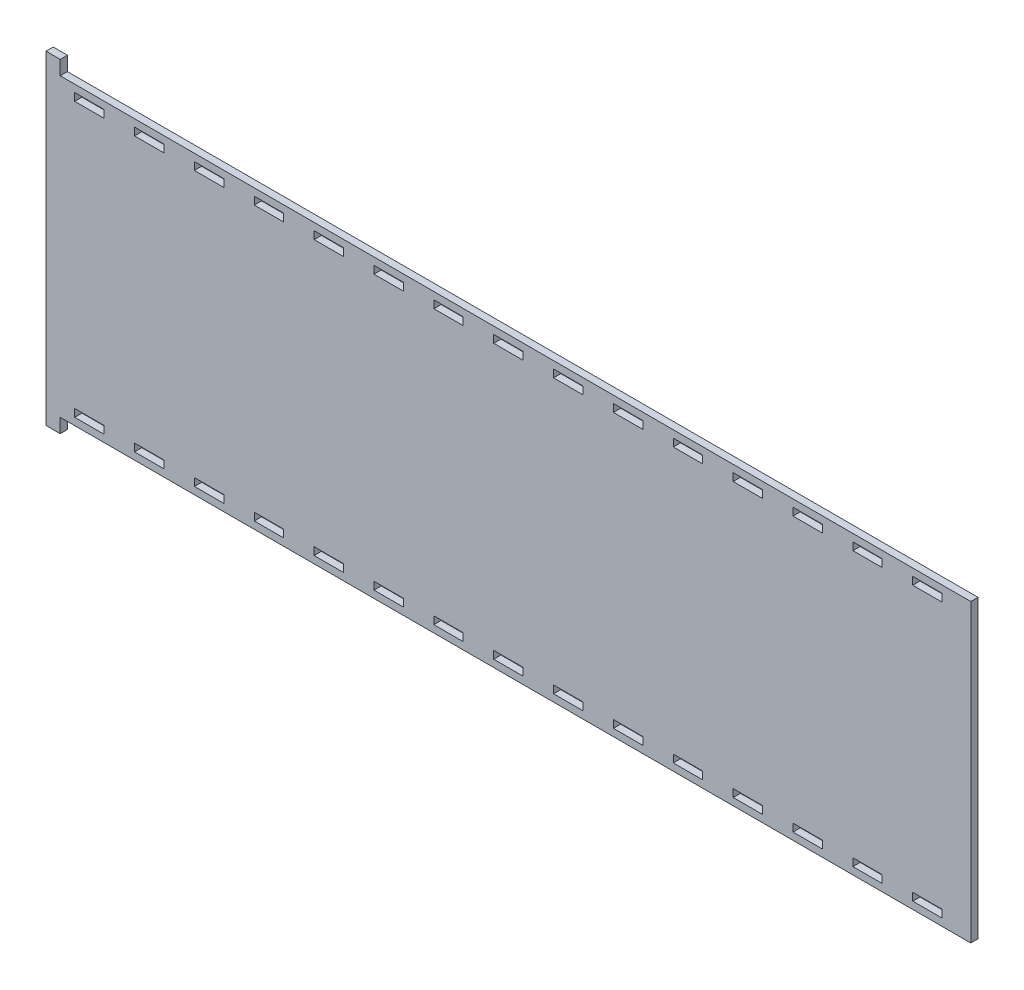
SolidWorks part; units mm, degrees
ref_plane "Front Plane" through (0, 0, 0) normal (0, 0, 1) x (1, 0, 0)
ref_plane "Top Plane" through (0, 0, 0) normal (0, 1, 0) x (1, 0, 0)
ref_plane "Right Plane" through (0, 0, 0) normal (1, 0, 0) x (0, 0, -1)
sketch "Sketch1" plane through (0, 0, 0) normal (0, 0, 1) x (1, 0, 0)
  line L8 (25.5, 123.5218) -> (12.6, 123.5218)
  line L9 (25.5, 120.1436) -> (25.5, 123.5218)
  line L10 (12.6, 120.1436) -> (25.5, 120.1436)
  line L11 (12.6, 123.5218) -> (12.6, 120.1436)
  line L16 (51.8071, 123.5218) -> (38.9071, 123.5218)
  line L17 (51.8071, 120.1436) -> (51.8071, 123.5218)
  line L18 (38.9071, 120.1436) -> (51.8071, 120.1436)
  line L19 (38.9071, 123.5218) -> (38.9071, 120.1436)
  line L24 (393.8, 123.5218) -> (380.9, 123.5218)
  line L25 (393.8, 120.1436) -> (393.8, 123.5218)
  line L26 (380.9, 120.1436) -> (393.8, 120.1436)
  line L27 (380.9, 123.5218) -> (380.9, 120.1436)
  line L32 (367.4929, 123.5218) -> (354.5929, 123.5218)
  line L33 (367.4929, 120.1436) -> (367.4929, 123.5218)
  line L34 (354.5929, 120.1436) -> (367.4929, 120.1436)
  line L35 (354.5929, 123.5218) -> (354.5929, 120.1436)
  line L40 (78.1143, 123.5218) -> (65.2143, 123.5218)
  line L41 (78.1143, 120.1436) -> (78.1143, 123.5218)
  line L42 (65.2143, 120.1436) -> (78.1143, 120.1436)
  line L43 (65.2143, 123.5218) -> (65.2143, 120.1436)
  line L48 (104.4214, 123.5218) -> (91.5214, 123.5218)
  line L49 (104.4214, 120.1436) -> (104.4214, 123.5218)
  line L50 (91.5214, 120.1436) -> (104.4214, 120.1436)
  line L51 (91.5214, 123.5218) -> (91.5214, 120.1436)
  line L56 (130.7286, 123.5218) -> (117.8286, 123.5218)
  line L57 (130.7286, 120.1436) -> (130.7286, 123.5218)
  line L58 (117.8286, 120.1436) -> (130.7286, 120.1436)
  line L59 (117.8286, 123.5218) -> (117.8286, 120.1436)
  line L64 (157.0357, 123.5218) -> (144.1357, 123.5218)
  line L65 (157.0357, 120.1436) -> (157.0357, 123.5218)
  line L66 (144.1357, 120.1436) -> (157.0357, 120.1436)
  line L67 (144.1357, 123.5218) -> (144.1357, 120.1436)
  line L72 (183.3429, 123.5218) -> (170.4429, 123.5218)
  line L73 (183.3429, 120.1436) -> (183.3429, 123.5218)
  line L74 (170.4429, 120.1436) -> (183.3429, 120.1436)
  line L75 (170.4429, 123.5218) -> (170.4429, 120.1436)
  line L80 (209.65, 123.5218) -> (196.75, 123.5218)
  line L81 (209.65, 120.1436) -> (209.65, 123.5218)
  line L82 (196.75, 120.1436) -> (209.65, 120.1436)
  line L83 (196.75, 123.5218) -> (196.75, 120.1436)
  line L88 (235.9571, 123.5218) -> (223.0571, 123.5218)
  line L89 (235.9571, 120.1436) -> (235.9571, 123.5218)
  line L90 (223.0571, 120.1436) -> (235.9571, 120.1436)
  line L91 (223.0571, 123.5218) -> (223.0571, 120.1436)
  line L96 (262.2643, 123.5218) -> (249.3643, 123.5218)
  line L97 (262.2643, 120.1436) -> (262.2643, 123.5218)
  line L98 (249.3643, 120.1436) -> (262.2643, 120.1436)
  line L99 (249.3643, 123.5218) -> (249.3643, 120.1436)
  line L104 (288.5714, 123.5218) -> (275.6714, 123.5218)
  line L105 (288.5714, 120.1436) -> (288.5714, 123.5218)
  line L106 (275.6714, 120.1436) -> (288.5714, 120.1436)
  line L107 (275.6714, 123.5218) -> (275.6714, 120.1436)
  line L112 (314.8786, 123.5218) -> (301.9786, 123.5218)
  line L113 (314.8786, 120.1436) -> (314.8786, 123.5218)
  line L114 (301.9786, 120.1436) -> (314.8786, 120.1436)
  line L115 (301.9786, 123.5218) -> (301.9786, 120.1436)
  line L120 (341.1857, 123.5218) -> (328.2857, 123.5218)
  line L121 (341.1857, 120.1436) -> (341.1857, 123.5218)
  line L122 (328.2857, 120.1436) -> (341.1857, 120.1436)
  line L123 (328.2857, 123.5218) -> (328.2857, 120.1436)
  line L128 (380.9, -0.1032) -> (393.8, -0.1032)
  line L129 (380.9, 3.275) -> (380.9, -0.1032)
  line L130 (393.8, 3.275) -> (380.9, 3.275)
  line L131 (393.8, -0.1032) -> (393.8, 3.275)
  line L136 (354.5929, -0.1032) -> (367.4929, -0.1032)
  line L137 (354.5929, 3.275) -> (354.5929, -0.1032)
  line L138 (367.4929, 3.275) -> (354.5929, 3.275)
  line L139 (367.4929, -0.1032) -> (367.4929, 3.275)
  line L144 (328.2857, -0.1032) -> (341.1857, -0.1032)
  line L145 (328.2857, 3.275) -> (328.2857, -0.1032)
  line L146 (341.1857, 3.275) -> (328.2857, 3.275)
  line L147 (341.1857, -0.1032) -> (341.1857, 3.275)
  line L152 (301.9786, -0.1032) -> (314.8786, -0.1032)
  line L153 (301.9786, 3.275) -> (301.9786, -0.1032)
  line L154 (314.8786, 3.275) -> (301.9786, 3.275)
  line L155 (314.8786, -0.1032) -> (314.8786, 3.275)
  line L160 (275.6714, -0.1032) -> (288.5714, -0.1032)
  line L161 (275.6714, 3.275) -> (275.6714, -0.1032)
  line L162 (288.5714, 3.275) -> (275.6714, 3.275)
  line L163 (288.5714, -0.1032) -> (288.5714, 3.275)
  line L168 (249.3643, -0.1032) -> (262.2643, -0.1032)
  line L169 (249.3643, 3.275) -> (249.3643, -0.1032)
  line L170 (262.2643, 3.275) -> (249.3643, 3.275)
  line L171 (262.2643, -0.1032) -> (262.2643, 3.275)
  line L176 (223.0571, -0.1032) -> (235.9571, -0.1032)
  line L177 (223.0571, 3.275) -> (223.0571, -0.1032)
  line L178 (235.9571, 3.275) -> (223.0571, 3.275)
  line L179 (235.9571, -0.1032) -> (235.9571, 3.275)
  line L184 (196.75, -0.1032) -> (209.65, -0.1032)
  line L185 (196.75, 3.275) -> (196.75, -0.1032)
  line L186 (209.65, 3.275) -> (196.75, 3.275)
  line L187 (209.65, -0.1032) -> (209.65, 3.275)
  line L192 (170.4429, -0.1032) -> (183.3429, -0.1032)
  line L193 (170.4429, 3.275) -> (170.4429, -0.1032)
  line L194 (183.3429, 3.275) -> (170.4429, 3.275)
  line L195 (183.3429, -0.1032) -> (183.3429, 3.275)
  line L200 (144.1357, -0.1032) -> (157.0357, -0.1032)
  line L201 (144.1357, 3.275) -> (144.1357, -0.1032)
  line L202 (157.0357, 3.275) -> (144.1357, 3.275)
  line L203 (157.0357, -0.1032) -> (157.0357, 3.275)
  line L208 (117.8286, -0.1032) -> (130.7286, -0.1032)
  line L209 (117.8286, 3.275) -> (117.8286, -0.1032)
  line L210 (130.7286, 3.275) -> (117.8286, 3.275)
  line L211 (130.7286, -0.1032) -> (130.7286, 3.275)
  line L216 (91.5214, -0.1032) -> (104.4214, -0.1032)
  line L217 (91.5214, 3.275) -> (91.5214, -0.1032)
  line L218 (104.4214, 3.275) -> (91.5214, 3.275)
  line L219 (104.4214, -0.1032) -> (104.4214, 3.275)
  line L224 (65.2143, -0.1032) -> (78.1143, -0.1032)
  line L225 (65.2143, 3.275) -> (65.2143, -0.1032)
  line L226 (78.1143, 3.275) -> (65.2143, 3.275)
  line L227 (78.1143, -0.1032) -> (78.1143, 3.275)
  line L232 (38.9071, -0.1032) -> (51.8071, -0.1032)
  line L233 (38.9071, 3.275) -> (38.9071, -0.1032)
  line L234 (51.8071, 3.275) -> (38.9071, 3.275)
  line L235 (51.8071, -0.1032) -> (51.8071, 3.275)
  line L240 (12.6, -0.1032) -> (25.5, -0.1032)
  line L241 (12.6, 3.275) -> (12.6, -0.1032)
  line L242 (25.5, 3.275) -> (12.6, 3.275)
  line L243 (25.5, -0.1032) -> (25.5, 3.275)
  line L256 (6.25, -9.525) -> (6.25, -3.2782)
  line L257 (6.25, -3.2782) -> (406.4, -3.2782)
  line L258 (406.4, -3.2782) -> (406.4, 126.6968)
  line L259 (406.4, 126.6968) -> (6.25, 126.6968)
  line L260 (6.25, 126.6968) -> (6.25, 132.9436)
  line L261 (6.25, 132.9436) -> (0, 132.9436)
  line L262 (0, 132.9436) -> (0, -9.525)
  line L263 (0, -9.525) -> (6.25, -9.525)
extrude "Boss-Extrude2" add sketch "Sketch1" along normal blind 3.175
sketch "DXF" plane through (0, 0, 0) normal (0, 0, 1) x (1, 0, 0)
  line L0 (25.3984, 123.4202) -> (12.7016, 123.4202)
  line L1 (12.7016, 123.4202) -> (12.7016, 120.2452)
  line L2 (12.7016, 120.2452) -> (25.3984, 120.2452)
  line L3 (25.3984, 120.2452) -> (25.3984, 123.4202)
  line L4 (51.7055, 123.4202) -> (39.0087, 123.4202)
  line L5 (39.0087, 123.4202) -> (39.0087, 120.2452)
  line L6 (39.0087, 120.2452) -> (51.7055, 120.2452)
  line L7 (51.7055, 120.2452) -> (51.7055, 123.4202)
  line L8 (25.5, 123.5218) -> (12.6, 123.5218) construction
  line L9 (25.5, 120.1436) -> (25.5, 123.5218) construction
  line L10 (12.6, 120.1436) -> (25.5, 120.1436) construction
  line L11 (12.6, 123.5218) -> (12.6, 120.1436) construction
  line L12 (393.6984, 123.4202) -> (381.0016, 123.4202)
  line L13 (381.0016, 123.4202) -> (381.0016, 120.2452)
  line L14 (381.0016, 120.2452) -> (393.6984, 120.2452)
  line L15 (393.6984, 120.2452) -> (393.6984, 123.4202)
  line L16 (51.8071, 123.5218) -> (38.9071, 123.5218) construction
  line L17 (51.8071, 120.1436) -> (51.8071, 123.5218) construction
  line L18 (38.9071, 120.1436) -> (51.8071, 120.1436) construction
  line L19 (38.9071, 123.5218) -> (38.9071, 120.1436) construction
  line L20 (367.3913, 123.4202) -> (354.6945, 123.4202)
  line L21 (354.6945, 123.4202) -> (354.6945, 120.2452)
  line L22 (354.6945, 120.2452) -> (367.3913, 120.2452)
  line L23 (367.3913, 120.2452) -> (367.3913, 123.4202)
  line L24 (393.8, 123.5218) -> (380.9, 123.5218) construction
  line L25 (393.8, 120.1436) -> (393.8, 123.5218) construction
  line L26 (380.9, 120.1436) -> (393.8, 120.1436) construction
  line L27 (380.9, 123.5218) -> (380.9, 120.1436) construction
  line L28 (78.0127, 123.4202) -> (65.3159, 123.4202)
  line L29 (65.3159, 123.4202) -> (65.3159, 120.2452)
  line L30 (65.3159, 120.2452) -> (78.0127, 120.2452)
  line L31 (78.0127, 120.2452) -> (78.0127, 123.4202)
  line L32 (367.4929, 123.5218) -> (354.5929, 123.5218) construction
  line L33 (367.4929, 120.1436) -> (367.4929, 123.5218) construction
  line L34 (354.5929, 120.1436) -> (367.4929, 120.1436) construction
  line L35 (354.5929, 123.5218) -> (354.5929, 120.1436) construction
  line L36 (104.3198, 123.4202) -> (91.623, 123.4202)
  line L37 (91.623, 123.4202) -> (91.623, 120.2452)
  line L38 (91.623, 120.2452) -> (104.3198, 120.2452)
  line L39 (104.3198, 120.2452) -> (104.3198, 123.4202)
  line L40 (78.1143, 123.5218) -> (65.2143, 123.5218) construction
  line L41 (78.1143, 120.1436) -> (78.1143, 123.5218) construction
  line L42 (65.2143, 120.1436) -> (78.1143, 120.1436) construction
  line L43 (65.2143, 123.5218) -> (65.2143, 120.1436) construction
  line L44 (130.627, 123.4202) -> (117.9302, 123.4202)
  line L45 (117.9302, 123.4202) -> (117.9302, 120.2452)
  line L46 (117.9302, 120.2452) -> (130.627, 120.2452)
  line L47 (130.627, 120.2452) -> (130.627, 123.4202)
  line L48 (104.4214, 123.5218) -> (91.5214, 123.5218) construction
  line L49 (104.4214, 120.1436) -> (104.4214, 123.5218) construction
  line L50 (91.5214, 120.1436) -> (104.4214, 120.1436) construction
  line L51 (91.5214, 123.5218) -> (91.5214, 120.1436) construction
  line L52 (156.9341, 123.4202) -> (144.2373, 123.4202)
  line L53 (144.2373, 123.4202) -> (144.2373, 120.2452)
  line L54 (144.2373, 120.2452) -> (156.9341, 120.2452)
  line L55 (156.9341, 120.2452) -> (156.9341, 123.4202)
  line L56 (130.7286, 123.5218) -> (117.8286, 123.5218) construction
  line L57 (130.7286, 120.1436) -> (130.7286, 123.5218) construction
  line L58 (117.8286, 120.1436) -> (130.7286, 120.1436) construction
  line L59 (117.8286, 123.5218) -> (117.8286, 120.1436) construction
  line L60 (183.2413, 123.4202) -> (170.5445, 123.4202)
  line L61 (170.5445, 123.4202) -> (170.5445, 120.2452)
  line L62 (170.5445, 120.2452) -> (183.2413, 120.2452)
  line L63 (183.2413, 120.2452) -> (183.2413, 123.4202)
  line L64 (157.0357, 123.5218) -> (144.1357, 123.5218) construction
  line L65 (157.0357, 120.1436) -> (157.0357, 123.5218) construction
  line L66 (144.1357, 120.1436) -> (157.0357, 120.1436) construction
  line L67 (144.1357, 123.5218) -> (144.1357, 120.1436) construction
  line L68 (209.5484, 123.4202) -> (196.8516, 123.4202)
  line L69 (196.8516, 123.4202) -> (196.8516, 120.2452)
  line L70 (196.8516, 120.2452) -> (209.5484, 120.2452)
  line L71 (209.5484, 120.2452) -> (209.5484, 123.4202)
  line L72 (183.3429, 123.5218) -> (170.4429, 123.5218) construction
  line L73 (183.3429, 120.1436) -> (183.3429, 123.5218) construction
  line L74 (170.4429, 120.1436) -> (183.3429, 120.1436) construction
  line L75 (170.4429, 123.5218) -> (170.4429, 120.1436) construction
  line L76 (235.8555, 123.4202) -> (223.1587, 123.4202)
  line L77 (223.1587, 123.4202) -> (223.1587, 120.2452)
  line L78 (223.1587, 120.2452) -> (235.8555, 120.2452)
  line L79 (235.8555, 120.2452) -> (235.8555, 123.4202)
  line L80 (209.65, 123.5218) -> (196.75, 123.5218) construction
  line L81 (209.65, 120.1436) -> (209.65, 123.5218) construction
  line L82 (196.75, 120.1436) -> (209.65, 120.1436) construction
  line L83 (196.75, 123.5218) -> (196.75, 120.1436) construction
  line L84 (262.1627, 123.4202) -> (249.4659, 123.4202)
  line L85 (249.4659, 123.4202) -> (249.4659, 120.2452)
  line L86 (249.4659, 120.2452) -> (262.1627, 120.2452)
  line L87 (262.1627, 120.2452) -> (262.1627, 123.4202)
  line L88 (235.9571, 123.5218) -> (223.0571, 123.5218) construction
  line L89 (235.9571, 120.1436) -> (235.9571, 123.5218) construction
  line L90 (223.0571, 120.1436) -> (235.9571, 120.1436) construction
  line L91 (223.0571, 123.5218) -> (223.0571, 120.1436) construction
  line L92 (288.4698, 123.4202) -> (275.773, 123.4202)
  line L93 (275.773, 123.4202) -> (275.773, 120.2452)
  line L94 (275.773, 120.2452) -> (288.4698, 120.2452)
  line L95 (288.4698, 120.2452) -> (288.4698, 123.4202)
  line L96 (262.2643, 123.5218) -> (249.3643, 123.5218) construction
  line L97 (262.2643, 120.1436) -> (262.2643, 123.5218) construction
  line L98 (249.3643, 120.1436) -> (262.2643, 120.1436) construction
  line L99 (249.3643, 123.5218) -> (249.3643, 120.1436) construction
  line L100 (314.777, 123.4202) -> (302.0802, 123.4202)
  line L101 (302.0802, 123.4202) -> (302.0802, 120.2452)
  line L102 (302.0802, 120.2452) -> (314.777, 120.2452)
  line L103 (314.777, 120.2452) -> (314.777, 123.4202)
  line L104 (288.5714, 123.5218) -> (275.6714, 123.5218) construction
  line L105 (288.5714, 120.1436) -> (288.5714, 123.5218) construction
  line L106 (275.6714, 120.1436) -> (288.5714, 120.1436) construction
  line L107 (275.6714, 123.5218) -> (275.6714, 120.1436) construction
  line L108 (341.0841, 123.4202) -> (328.3873, 123.4202)
  line L109 (328.3873, 123.4202) -> (328.3873, 120.2452)
  line L110 (328.3873, 120.2452) -> (341.0841, 120.2452)
  line L111 (341.0841, 120.2452) -> (341.0841, 123.4202)
  line L112 (314.8786, 123.5218) -> (301.9786, 123.5218) construction
  line L113 (314.8786, 120.1436) -> (314.8786, 123.5218) construction
  line L114 (301.9786, 120.1436) -> (314.8786, 120.1436) construction
  line L115 (301.9786, 123.5218) -> (301.9786, 120.1436) construction
  line L116 (381.0016, -0.0016) -> (393.6984, -0.0016)
  line L117 (393.6984, -0.0016) -> (393.6984, 3.1734)
  line L118 (393.6984, 3.1734) -> (381.0016, 3.1734)
  line L119 (381.0016, 3.1734) -> (381.0016, -0.0016)
  line L120 (341.1857, 123.5218) -> (328.2857, 123.5218) construction
  line L121 (341.1857, 120.1436) -> (341.1857, 123.5218) construction
  line L122 (328.2857, 120.1436) -> (341.1857, 120.1436) construction
  line L123 (328.2857, 123.5218) -> (328.2857, 120.1436) construction
  line L124 (354.6945, -0.0016) -> (367.3913, -0.0016)
  line L125 (367.3913, -0.0016) -> (367.3913, 3.1734)
  line L126 (367.3913, 3.1734) -> (354.6945, 3.1734)
  line L127 (354.6945, 3.1734) -> (354.6945, -0.0016)
  line L128 (380.9, -0.1032) -> (393.8, -0.1032) construction
  line L129 (380.9, 3.275) -> (380.9, -0.1032) construction
  line L130 (393.8, 3.275) -> (380.9, 3.275) construction
  line L131 (393.8, -0.1032) -> (393.8, 3.275) construction
  line L132 (328.3873, -0.0016) -> (341.0841, -0.0016)
  line L133 (341.0841, -0.0016) -> (341.0841, 3.1734)
  line L134 (341.0841, 3.1734) -> (328.3873, 3.1734)
  line L135 (328.3873, 3.1734) -> (328.3873, -0.0016)
  line L136 (354.5929, -0.1032) -> (367.4929, -0.1032) construction
  line L137 (354.5929, 3.275) -> (354.5929, -0.1032) construction
  line L138 (367.4929, 3.275) -> (354.5929, 3.275) construction
  line L139 (367.4929, -0.1032) -> (367.4929, 3.275) construction
  line L140 (302.0802, -0.0016) -> (314.777, -0.0016)
  line L141 (314.777, -0.0016) -> (314.777, 3.1734)
  line L142 (314.777, 3.1734) -> (302.0802, 3.1734)
  line L143 (302.0802, 3.1734) -> (302.0802, -0.0016)
  line L144 (328.2857, -0.1032) -> (341.1857, -0.1032) construction
  line L145 (328.2857, 3.275) -> (328.2857, -0.1032) construction
  line L146 (341.1857, 3.275) -> (328.2857, 3.275) construction
  line L147 (341.1857, -0.1032) -> (341.1857, 3.275) construction
  line L148 (275.773, -0.0016) -> (288.4698, -0.0016)
  line L149 (288.4698, -0.0016) -> (288.4698, 3.1734)
  line L150 (288.4698, 3.1734) -> (275.773, 3.1734)
  line L151 (275.773, 3.1734) -> (275.773, -0.0016)
  line L152 (301.9786, -0.1032) -> (314.8786, -0.1032) construction
  line L153 (301.9786, 3.275) -> (301.9786, -0.1032) construction
  line L154 (314.8786, 3.275) -> (301.9786, 3.275) construction
  line L155 (314.8786, -0.1032) -> (314.8786, 3.275) construction
  line L156 (249.4659, -0.0016) -> (262.1627, -0.0016)
  line L157 (262.1627, -0.0016) -> (262.1627, 3.1734)
  line L158 (262.1627, 3.1734) -> (249.4659, 3.1734)
  line L159 (249.4659, 3.1734) -> (249.4659, -0.0016)
  line L160 (275.6714, -0.1032) -> (288.5714, -0.1032) construction
  line L161 (275.6714, 3.275) -> (275.6714, -0.1032) construction
  line L162 (288.5714, 3.275) -> (275.6714, 3.275) construction
  line L163 (288.5714, -0.1032) -> (288.5714, 3.275) construction
  line L164 (223.1587, -0.0016) -> (235.8555, -0.0016)
  line L165 (235.8555, -0.0016) -> (235.8555, 3.1734)
  line L166 (235.8555, 3.1734) -> (223.1587, 3.1734)
  line L167 (223.1587, 3.1734) -> (223.1587, -0.0016)
  line L168 (249.3643, -0.1032) -> (262.2643, -0.1032) construction
  line L169 (249.3643, 3.275) -> (249.3643, -0.1032) construction
  line L170 (262.2643, 3.275) -> (249.3643, 3.275) construction
  line L171 (262.2643, -0.1032) -> (262.2643, 3.275) construction
  line L172 (196.8516, -0.0016) -> (209.5484, -0.0016)
  line L173 (209.5484, -0.0016) -> (209.5484, 3.1734)
  line L174 (209.5484, 3.1734) -> (196.8516, 3.1734)
  line L175 (196.8516, 3.1734) -> (196.8516, -0.0016)
  line L176 (223.0571, -0.1032) -> (235.9571, -0.1032) construction
  line L177 (223.0571, 3.275) -> (223.0571, -0.1032) construction
  line L178 (235.9571, 3.275) -> (223.0571, 3.275) construction
  line L179 (235.9571, -0.1032) -> (235.9571, 3.275) construction
  line L180 (170.5445, -0.0016) -> (183.2413, -0.0016)
  line L181 (183.2413, -0.0016) -> (183.2413, 3.1734)
  line L182 (183.2413, 3.1734) -> (170.5445, 3.1734)
  line L183 (170.5445, 3.1734) -> (170.5445, -0.0016)
  line L184 (196.75, -0.1032) -> (209.65, -0.1032) construction
  line L185 (196.75, 3.275) -> (196.75, -0.1032) construction
  line L186 (209.65, 3.275) -> (196.75, 3.275) construction
  line L187 (209.65, -0.1032) -> (209.65, 3.275) construction
  line L188 (144.2373, -0.0016) -> (156.9341, -0.0016)
  line L189 (156.9341, -0.0016) -> (156.9341, 3.1734)
  line L190 (156.9341, 3.1734) -> (144.2373, 3.1734)
  line L191 (144.2373, 3.1734) -> (144.2373, -0.0016)
  line L192 (170.4429, -0.1032) -> (183.3429, -0.1032) construction
  line L193 (170.4429, 3.275) -> (170.4429, -0.1032) construction
  line L194 (183.3429, 3.275) -> (170.4429, 3.275) construction
  line L195 (183.3429, -0.1032) -> (183.3429, 3.275) construction
  line L196 (117.9302, -0.0016) -> (130.627, -0.0016)
  line L197 (130.627, -0.0016) -> (130.627, 3.1734)
  line L198 (130.627, 3.1734) -> (117.9302, 3.1734)
  line L199 (117.9302, 3.1734) -> (117.9302, -0.0016)
  line L200 (144.1357, -0.1032) -> (157.0357, -0.1032) construction
  line L201 (144.1357, 3.275) -> (144.1357, -0.1032) construction
  line L202 (157.0357, 3.275) -> (144.1357, 3.275) construction
  line L203 (157.0357, -0.1032) -> (157.0357, 3.275) construction
  line L204 (91.623, -0.0016) -> (104.3198, -0.0016)
  line L205 (104.3198, -0.0016) -> (104.3198, 3.1734)
  line L206 (104.3198, 3.1734) -> (91.623, 3.1734)
  line L207 (91.623, 3.1734) -> (91.623, -0.0016)
  line L208 (117.8286, -0.1032) -> (130.7286, -0.1032) construction
  line L209 (117.8286, 3.275) -> (117.8286, -0.1032) construction
  line L210 (130.7286, 3.275) -> (117.8286, 3.275) construction
  line L211 (130.7286, -0.1032) -> (130.7286, 3.275) construction
  line L212 (65.3159, -0.0016) -> (78.0127, -0.0016)
  line L213 (78.0127, -0.0016) -> (78.0127, 3.1734)
  line L214 (78.0127, 3.1734) -> (65.3159, 3.1734)
  line L215 (65.3159, 3.1734) -> (65.3159, -0.0016)
  line L216 (91.5214, -0.1032) -> (104.4214, -0.1032) construction
  line L217 (91.5214, 3.275) -> (91.5214, -0.1032) construction
  line L218 (104.4214, 3.275) -> (91.5214, 3.275) construction
  line L219 (104.4214, -0.1032) -> (104.4214, 3.275) construction
  line L220 (39.0087, -0.0016) -> (51.7055, -0.0016)
  line L221 (51.7055, -0.0016) -> (51.7055, 3.1734)
  line L222 (51.7055, 3.1734) -> (39.0087, 3.1734)
  line L223 (39.0087, 3.1734) -> (39.0087, -0.0016)
  line L224 (65.2143, -0.1032) -> (78.1143, -0.1032) construction
  line L225 (65.2143, 3.275) -> (65.2143, -0.1032) construction
  line L226 (78.1143, 3.275) -> (65.2143, 3.275) construction
  line L227 (78.1143, -0.1032) -> (78.1143, 3.275) construction
  line L228 (12.7016, -0.0016) -> (25.3984, -0.0016)
  line L229 (25.3984, -0.0016) -> (25.3984, 3.1734)
  line L230 (25.3984, 3.1734) -> (12.7016, 3.1734)
  line L231 (12.7016, 3.1734) -> (12.7016, -0.0016)
  line L232 (38.9071, -0.1032) -> (51.8071, -0.1032) construction
  line L233 (38.9071, 3.275) -> (38.9071, -0.1032) construction
  line L234 (51.8071, 3.275) -> (38.9071, 3.275) construction
  line L235 (51.8071, -0.1032) -> (51.8071, 3.275) construction
  line L236 (-0.1016, 133.0452) -> (-0.1016, -9.6266)
  line L237 (-0.1016, -9.6266) -> (6.3516, -9.6266)
  line L238 (6.3516, -9.6266) -> (6.3516, -3.3798)
  line L239 (6.3516, -3.3798) -> (406.5016, -3.3798)
  line L240 (12.6, -0.1032) -> (25.5, -0.1032) construction
  line L241 (12.6, 3.275) -> (12.6, -0.1032) construction
  line L242 (25.5, 3.275) -> (12.6, 3.275) construction
  line L243 (25.5, -0.1032) -> (25.5, 3.275) construction
  line L244 (406.5016, -3.3798) -> (406.5016, 126.7984)
  line L245 (406.5016, 126.7984) -> (6.3516, 126.7984)
  line L246 (6.3516, 126.7984) -> (6.3516, 133.0452)
  line L247 (6.3516, 133.0452) -> (-0.1016, 133.0452)
  line L256 (6.25, -9.525) -> (6.25, -3.2782) construction
  line L257 (6.25, -3.2782) -> (406.4, -3.2782) construction
  line L258 (406.4, -3.2782) -> (406.4, 126.6968) construction
  line L259 (406.4, 126.6968) -> (6.25, 126.6968) construction
  line L260 (6.25, 126.6968) -> (6.25, 132.9436) construction
  line L261 (6.25, 132.9436) -> (0, 132.9436) construction
  line L262 (0, 132.9436) -> (0, -9.525) construction
  line L263 (0, -9.525) -> (6.25, -9.525) construction
  dimension "D1" = 0.1016
  dimension "D2" = 0.1016
extrude "DXF-Extrude" [suppressed] add sketch "DXF" along normal blind 3.175 separate body
